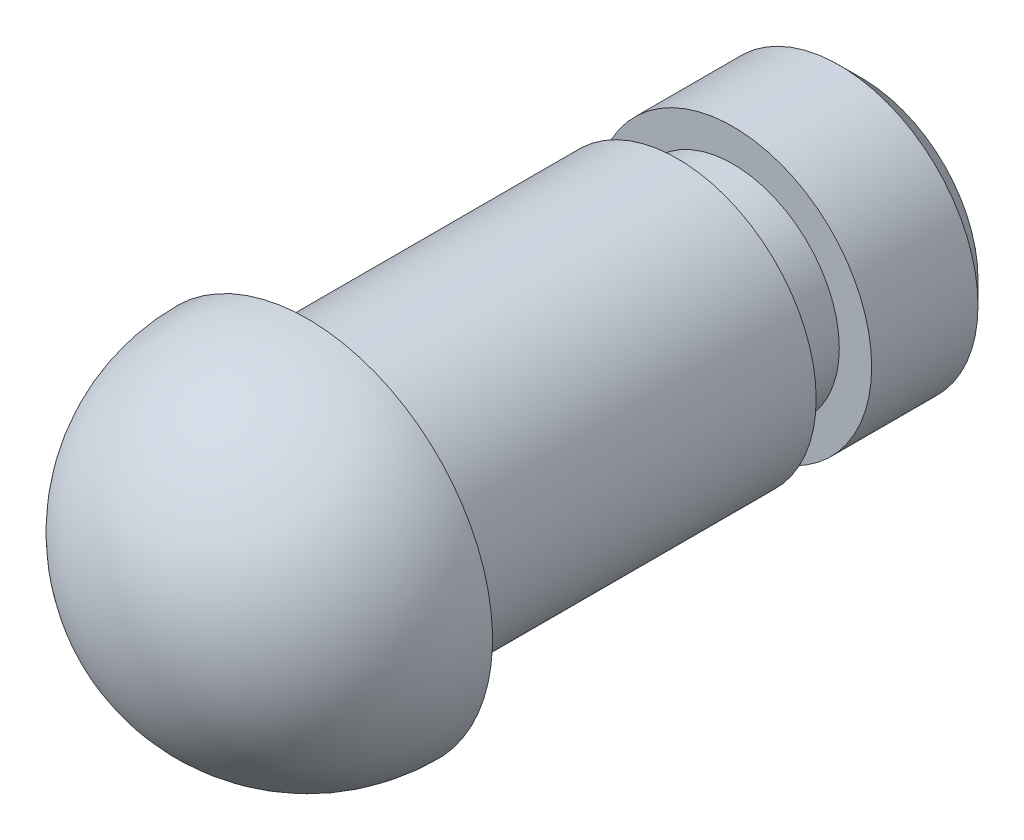
SolidWorks part; units mm, degrees
ref_plane "Front Plane" through (0, 0, 0) normal (0, 0, 1) x (1, 0, 0)
ref_plane "Top Plane" through (0, 0, 0) normal (0, 1, 0) x (1, 0, 0)
ref_plane "Right Plane" through (0, 0, 0) normal (1, 0, 0) x (0, 0, -1)
sketch "Sketch1" plane through (0, 0, 0) normal (0, 0, 1) x (1, 0, 0)
  circle A0 centre (0, 0) radius 1.5
  dimension "D1" = 3
extrude "Boss-Extrude1" add sketch "Sketch1" along normal blind 1.4
sketch "Sketch2" plane through (0, 0, 1.4) normal (0, 0, 1) x (1, 0, 0)
  circle A0 centre (0, 0) radius 1.15
  dimension "D1" = 2.3
extrude "Boss-Extrude2" add sketch "Sketch2" along normal blind 0.6
sketch "Sketch3" plane through (0, 0, 2) normal (0, 0, 1) x (1, 0, 0)
  circle A0 centre (0, 0) radius 1.5
  dimension "D1" = 3
extrude "Boss-Extrude3" add sketch "Sketch3" along normal blind 4
sketch "Sketch4" plane through (0, 0, 6) normal (0, 0, 1) x (1, 0, 0)
  line L0 (0, 2) -> (0, -2)
  arc A0 (0, -2) -> (0, 2) centre (0, 0) ccw
  dimension "D1" = 4
revolve "Revolve1" add sketch "Sketch4" angle 180 about L0
chamfer "Chamfer1" distance 0.25 angle 45 1 edges at (1.5, 0, 0)
